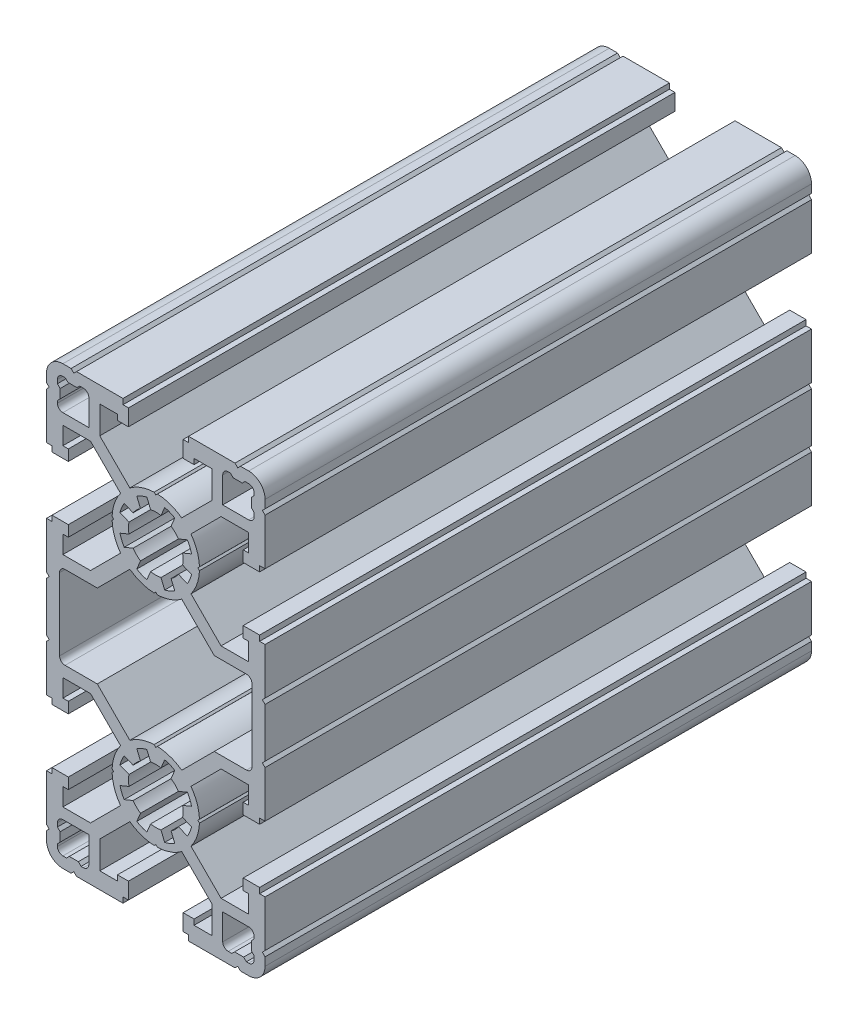
SolidWorks part; units mm, degrees
ref_plane "Ön Düzlem" through (0, 0, 0) normal (0, 0, 1) x (1, 0, 0)
ref_plane "Üst Düzlem" through (0, 0, 0) normal (0, 1, 0) x (1, 0, 0)
ref_plane "Sağ Düzlem" through (0, 0, 0) normal (1, 0, 0) x (0, 0, -1)
ref_plane "Düzlem1" through (0, 0, 100) normal (0, 0, 1) x (1, 0, 0)
sketch "Çizim1" plane through (0, 0, 100) normal (0, 0, 1) x (1, 0, 0)
  line L0 (1.6307, -26.5501) -> (0.9509, -24.9088)
  line L1 (-0.9509, -24.9088) -> (-1.6307, -26.5501)
  line L2 (-3.4785, -25.7847) -> (-2.7986, -24.1434)
  line L3 (-4.1434, -22.7986) -> (-5.7847, -23.4785)
  line L4 (-6.5501, -21.6307) -> (-4.9088, -20.9509)
  line L5 (-4.9088, -19.0491) -> (-6.5501, -18.3693)
  line L6 (-5.7847, -16.5215) -> (-4.1434, -17.2014)
  line L7 (-2.7986, -15.8566) -> (-3.4785, -14.2153)
  line L8 (-1.6307, -13.4499) -> (-0.9509, -15.0912)
  line L9 (0.9509, -15.0912) -> (1.6307, -13.4499)
  line L10 (3.4785, -14.2153) -> (2.7986, -15.8566)
  line L11 (4.1434, -17.2014) -> (5.7847, -16.5215)
  line L12 (6.5501, -18.3693) -> (4.9088, -19.0491)
  line L13 (4.9088, -20.9509) -> (6.5501, -21.6307)
  line L14 (5.7847, -23.4785) -> (4.1434, -22.7986)
  line L15 (2.7986, -24.1434) -> (3.4785, -25.7847)
  line L16 (17, -38) -> (16.5784, -38)
  line L17 (16.5784, -38) -> (16.0784, -37.5)
  line L18 (16.0784, -37.5) -> (14.4216, -37.5)
  line L19 (14.4216, -37.5) -> (13.9216, -38)
  line L20 (13.9216, -38) -> (13.25, -38)
  line L21 (12.25, -37) -> (12.25, -32.25)
  line L22 (12.25, -32.25) -> (17, -32.25)
  line L23 (18, -33.25) -> (18, -33.6716)
  line L24 (18, -33.6716) -> (17.5, -34.1716)
  line L25 (17.5, -34.1716) -> (17.5, -35.8284)
  line L26 (17.5, -35.8284) -> (18, -36.3284)
  line L27 (18, -36.3284) -> (18, -37)
  line L28 (-18, -37) -> (-18, -36.5784)
  line L29 (-18, -36.5784) -> (-17.5, -36.0784)
  line L30 (-17.5, -36.0784) -> (-17.5, -34.4216)
  line L31 (-17.5, -34.4216) -> (-18, -33.9216)
  line L32 (-18, -33.9216) -> (-18, -33.25)
  line L33 (-17, -32.25) -> (-12.25, -32.25)
  line L34 (-12.25, -32.25) -> (-12.25, -37)
  line L35 (-13.25, -38) -> (-13.6716, -38)
  line L36 (-13.6716, -38) -> (-14.1716, -37.5)
  line L37 (-14.1716, -37.5) -> (-15.8284, -37.5)
  line L38 (-15.8284, -37.5) -> (-16.3284, -38)
  line L39 (-16.3284, -38) -> (-17, -38)
  line L40 (5, 36) -> (7, 36)
  line L41 (7, 36) -> (7, 37)
  line L42 (7, 37) -> (10.25, 37)
  line L43 (10.25, 37) -> (10.25, 31.9471)
  line L44 (10.25, 31.9471) -> (4.7443, 26.4414)
  line L45 (0.3064, 27.9941) -> (0, 27.7)
  line L46 (0, 27.7) -> (-0.3064, 27.9941)
  line L47 (-4.7443, 26.4414) -> (-10.25, 31.9471)
  line L48 (-10.25, 31.9471) -> (-10.25, 37)
  line L49 (-10.25, 37) -> (-7, 37)
  line L50 (-7, 37) -> (-7, 36)
  line L51 (-7, 36) -> (-5, 36)
  line L52 (-5, 36) -> (-5, 39)
  line L53 (-5, 39) -> (-6, 39)
  line L54 (-6, 39) -> (-6, 40)
  line L55 (-6, 40) -> (-14.5, 40)
  line L56 (-14.5, 40) -> (-15, 39.5)
  line L57 (-15, 39.5) -> (-15.5, 40)
  line L58 (-15.5, 40) -> (-17, 40)
  line L59 (-20, 37) -> (-20, 35.5)
  line L60 (-20, 35.5) -> (-19.5, 35)
  line L61 (-19.5, 35) -> (-20, 34.5)
  line L62 (-20, 34.5) -> (-20, 26)
  line L63 (-20, 26) -> (-19, 26)
  line L64 (-19, 26) -> (-19, 25)
  line L65 (-19, 25) -> (-16, 25)
  line L66 (-16, 25) -> (-16, 27)
  line L67 (-16, 27) -> (-17, 27)
  line L68 (-17, 27) -> (-17, 30.25)
  line L69 (-17, 30.25) -> (-11.9471, 30.25)
  line L70 (-11.9471, 30.25) -> (-6.4414, 24.7443)
  line L71 (-7.9941, 20.3064) -> (-7.7, 20)
  line L72 (-7.7, 20) -> (-7.9941, 19.6936)
  line L73 (-6.4414, 15.2557) -> (-11.9471, 9.75)
  line L74 (-11.9471, 9.75) -> (-17, 9.75)
  line L75 (-17, 9.75) -> (-17, 13)
  line L76 (-17, 13) -> (-16, 13)
  line L77 (-16, 13) -> (-16, 15)
  line L78 (-16, 15) -> (-19, 15)
  line L79 (-19, 15) -> (-19, 14)
  line L80 (-19, 14) -> (-20, 14)
  line L81 (-20, 14) -> (-20, 5.5)
  line L82 (-20, 5.5) -> (-19.5, 5)
  line L83 (-19.5, 5) -> (-20, 4.5)
  line L84 (-20, 4.5) -> (-20, -4.5)
  line L85 (-20, -4.5) -> (-19.5, -5)
  line L86 (-19.5, -5) -> (-20, -5.5)
  line L87 (-20, -5.5) -> (-20, -14)
  line L88 (-20, -14) -> (-19, -14)
  line L89 (-19, -14) -> (-19, -15)
  line L90 (-19, -15) -> (-16, -15)
  line L91 (-16, -15) -> (-16, -13)
  line L92 (-16, -13) -> (-17, -13)
  line L93 (-17, -13) -> (-17, -9.75)
  line L94 (-17, -9.75) -> (-11.9471, -9.75)
  line L95 (-11.9471, -9.75) -> (-6.4414, -15.2557)
  line L96 (-7.9941, -19.6936) -> (-7.7, -20)
  line L97 (-7.7, -20) -> (-7.9941, -20.3064)
  line L98 (-6.4414, -24.7443) -> (-11.9471, -30.25)
  line L99 (-11.9471, -30.25) -> (-17, -30.25)
  line L100 (-17, -30.25) -> (-17, -27)
  line L101 (-17, -27) -> (-16, -27)
  line L102 (-16, -27) -> (-16, -25)
  line L103 (-16, -25) -> (-19, -25)
  line L104 (-19, -25) -> (-19, -26)
  line L105 (-19, -26) -> (-20, -26)
  line L106 (-20, -26) -> (-20, -34.5)
  line L107 (-20, -34.5) -> (-19.5, -35)
  line L108 (-19.5, -35) -> (-20, -35.5)
  line L109 (-20, -35.5) -> (-20, -37)
  line L110 (-17, -40) -> (-15.5, -40)
  line L111 (-15.5, -40) -> (-15, -39.5)
  line L112 (-15, -39.5) -> (-14.5, -40)
  line L113 (-14.5, -40) -> (-6, -40)
  line L114 (-6, -40) -> (-6, -39)
  line L115 (-6, -39) -> (-5, -39)
  line L116 (-5, -39) -> (-5, -36)
  line L117 (-5, -36) -> (-7, -36)
  line L118 (-7, -36) -> (-7, -37)
  line L119 (-7, -37) -> (-10.25, -37)
  line L120 (-10.25, -37) -> (-10.25, -31.9471)
  line L121 (-10.25, -31.9471) -> (-4.7443, -26.4414)
  line L122 (-0.3064, -27.9941) -> (0, -27.7)
  line L123 (0, -27.7) -> (0.3064, -27.9941)
  line L124 (4.7443, -26.4414) -> (10.25, -31.9471)
  line L125 (10.25, -31.9471) -> (10.25, -37)
  line L126 (10.25, -37) -> (7, -37)
  line L127 (7, -37) -> (7, -36)
  line L128 (7, -36) -> (5, -36)
  line L129 (5, -36) -> (5, -39)
  line L130 (5, -39) -> (6, -39)
  line L131 (6, -39) -> (6, -40)
  line L132 (6, -40) -> (14.5, -40)
  line L133 (14.5, -40) -> (15, -39.5)
  line L134 (15, -39.5) -> (15.5, -40)
  line L135 (15.5, -40) -> (17, -40)
  line L136 (20, -37) -> (20, -35.5)
  line L137 (20, -35.5) -> (19.5, -35)
  line L138 (19.5, -35) -> (20, -34.5)
  line L139 (20, -34.5) -> (20, -26)
  line L140 (20, -26) -> (19, -26)
  line L141 (19, -26) -> (19, -25)
  line L142 (19, -25) -> (16, -25)
  line L143 (16, -25) -> (16, -27)
  line L144 (16, -27) -> (17, -27)
  line L145 (17, -27) -> (17, -30.25)
  line L146 (17, -30.25) -> (11.9471, -30.25)
  line L147 (11.9471, -30.25) -> (6.4414, -24.7443)
  line L148 (7.9941, -20.3064) -> (7.7, -20)
  line L149 (7.7, -20) -> (7.9941, -19.6936)
  line L150 (6.4414, -15.2557) -> (11.9471, -9.75)
  line L151 (11.9471, -9.75) -> (17, -9.75)
  line L152 (17, -9.75) -> (17, -13)
  line L153 (17, -13) -> (16, -13)
  line L154 (16, -13) -> (16, -15)
  line L155 (16, -15) -> (19, -15)
  line L156 (19, -15) -> (19, -14)
  line L157 (19, -14) -> (20, -14)
  line L158 (20, -14) -> (20, -5.5)
  line L159 (20, -5.5) -> (19.5, -5)
  line L160 (19.5, -5) -> (20, -4.5)
  line L161 (20, -4.5) -> (20, 4.5)
  line L162 (20, 4.5) -> (19.5, 5)
  line L163 (19.5, 5) -> (20, 5.5)
  line L164 (20, 5.5) -> (20, 14)
  line L165 (20, 14) -> (19, 14)
  line L166 (19, 14) -> (19, 15)
  line L167 (19, 15) -> (16, 15)
  line L168 (16, 15) -> (16, 13)
  line L169 (16, 13) -> (17, 13)
  line L170 (17, 13) -> (17, 9.75)
  line L171 (17, 9.75) -> (11.9471, 9.75)
  line L172 (11.9471, 9.75) -> (6.4414, 15.2557)
  line L173 (7.9941, 19.6936) -> (7.7, 20)
  line L174 (7.7, 20) -> (7.9941, 20.3064)
  line L175 (6.4414, 24.7443) -> (11.9471, 30.25)
  line L176 (11.9471, 30.25) -> (17, 30.25)
  line L177 (17, 30.25) -> (17, 27)
  line L178 (17, 27) -> (16, 27)
  line L179 (16, 27) -> (16, 25)
  line L180 (16, 25) -> (19, 25)
  line L181 (19, 25) -> (19, 26)
  line L182 (19, 26) -> (20, 26)
  line L183 (20, 26) -> (20, 34.5)
  line L184 (20, 34.5) -> (19.5, 35)
  line L185 (19.5, 35) -> (20, 35.5)
  line L186 (20, 35.5) -> (20, 37)
  line L187 (17, 40) -> (15.5, 40)
  line L188 (15.5, 40) -> (15, 39.5)
  line L189 (15, 39.5) -> (14.5, 40)
  line L190 (14.5, 40) -> (6, 40)
  line L191 (6, 40) -> (6, 39)
  line L192 (6, 39) -> (5, 39)
  line L193 (5, 39) -> (5, 36)
  line L194 (18, 37) -> (18, 36.5784)
  line L195 (18, 36.5784) -> (17.5, 36.0784)
  line L196 (17.5, 36.0784) -> (17.5, 34.4216)
  line L197 (17.5, 34.4216) -> (18, 33.9216)
  line L198 (18, 33.9216) -> (18, 33.25)
  line L199 (17, 32.25) -> (12.25, 32.25)
  line L200 (12.25, 32.25) -> (12.25, 37)
  line L201 (13.25, 38) -> (13.6716, 38)
  line L202 (13.6716, 38) -> (14.1716, 37.5)
  line L203 (14.1716, 37.5) -> (15.8284, 37.5)
  line L204 (15.8284, 37.5) -> (16.3284, 38)
  line L205 (16.3284, 38) -> (17, 38)
  line L206 (-17, 38) -> (-16.5784, 38)
  line L207 (-16.5784, 38) -> (-16.0784, 37.5)
  line L208 (-16.0784, 37.5) -> (-14.4216, 37.5)
  line L209 (-14.4216, 37.5) -> (-13.9216, 38)
  line L210 (-13.9216, 38) -> (-13.25, 38)
  line L211 (-12.25, 37) -> (-12.25, 32.25)
  line L212 (-12.25, 32.25) -> (-17, 32.25)
  line L213 (-18, 33.25) -> (-18, 33.6716)
  line L214 (-18, 33.6716) -> (-17.5, 34.1716)
  line L215 (-17.5, 34.1716) -> (-17.5, 35.8284)
  line L216 (-17.5, 35.8284) -> (-18, 36.3284)
  line L217 (-18, 36.3284) -> (-18, 37)
  line L218 (17.6, 6.6) -> (17.6, -6.6)
  line L219 (16.6, -7.6) -> (10.7029, -7.6)
  line L220 (10.7029, -7.6) -> (4.7443, -13.5586)
  line L221 (0.3064, -12.0059) -> (0, -12.3)
  line L222 (0, -12.3) -> (-0.3064, -12.0059)
  line L223 (-4.7443, -13.5586) -> (-10.7029, -7.6)
  line L224 (-10.7029, -7.6) -> (-16.6, -7.6)
  line L225 (-17.6, -6.6) -> (-17.6, 6.6)
  line L226 (-16.6, 7.6) -> (-10.7029, 7.6)
  line L227 (-10.7029, 7.6) -> (-4.7443, 13.5586)
  line L228 (-0.3064, 12.0059) -> (0, 12.3)
  line L229 (0, 12.3) -> (0.3064, 12.0059)
  line L230 (4.7443, 13.5586) -> (10.7029, 7.6)
  line L231 (10.7029, 7.6) -> (16.6, 7.6)
  line L232 (1.6307, 13.4499) -> (0.9509, 15.0912)
  line L233 (-0.9509, 15.0912) -> (-1.6307, 13.4499)
  line L234 (-3.4785, 14.2153) -> (-2.7986, 15.8566)
  line L235 (-4.1434, 17.2014) -> (-5.7847, 16.5215)
  line L236 (-6.5501, 18.3693) -> (-4.9088, 19.0491)
  line L237 (-4.9088, 20.9509) -> (-6.5501, 21.6307)
  line L238 (-5.7847, 23.4785) -> (-4.1434, 22.7986)
  line L239 (-2.7986, 24.1434) -> (-3.4785, 25.7847)
  line L240 (-1.6307, 26.5501) -> (-0.9509, 24.9088)
  line L241 (0.9509, 24.9088) -> (1.6307, 26.5501)
  line L242 (3.4785, 25.7847) -> (2.7986, 24.1434)
  line L243 (4.1434, 22.7986) -> (5.7847, 23.4785)
  line L244 (6.5501, 21.6307) -> (4.9088, 20.9509)
  line L245 (4.9088, 19.0491) -> (6.5501, 18.3693)
  line L246 (5.7847, 16.5215) -> (4.1434, 17.2014)
  line L247 (2.7986, 15.8566) -> (3.4785, 14.2153)
  arc A0 (3.4785, -25.7847) -> (1.6307, -26.5501) centre (0, -20) cw
  arc A1 (0.9509, -24.9088) -> (-0.9509, -24.9088) centre (0, -20) cw
  arc A2 (-1.6307, -26.5501) -> (-3.4785, -25.7847) centre (0, -20) cw
  arc A3 (-2.7986, -24.1434) -> (-4.1434, -22.7986) centre (0, -20) cw
  arc A4 (-5.7847, -23.4785) -> (-6.5501, -21.6307) centre (0, -20) cw
  arc A5 (-4.9088, -20.9509) -> (-4.9088, -19.0491) centre (0, -20) cw
  arc A6 (-6.5501, -18.3693) -> (-5.7847, -16.5215) centre (0, -20) cw
  arc A7 (-4.1434, -17.2014) -> (-2.7986, -15.8566) centre (0, -20) cw
  arc A8 (-3.4785, -14.2153) -> (-1.6307, -13.4499) centre (0, -20) cw
  arc A9 (-0.9509, -15.0912) -> (0.9509, -15.0912) centre (0, -20) cw
  arc A10 (1.6307, -13.4499) -> (3.4785, -14.2153) centre (0, -20) cw
  arc A11 (2.7986, -15.8566) -> (4.1434, -17.2014) centre (0, -20) cw
  arc A12 (5.7847, -16.5215) -> (6.5501, -18.3693) centre (0, -20) cw
  arc A13 (4.9088, -19.0491) -> (4.9088, -20.9509) centre (0, -20) cw
  arc A14 (6.5501, -21.6307) -> (5.7847, -23.4785) centre (0, -20) cw
  arc A15 (4.1434, -22.7986) -> (2.7986, -24.1434) centre (0, -20) cw
  arc A16 (13.25, -38) -> (12.25, -37) centre (13.25, -37) cw
  arc A17 (17, -32.25) -> (18, -33.25) centre (17, -33.25) cw
  arc A18 (18, -37) -> (17, -38) centre (17, -37) cw
  arc A19 (-18, -33.25) -> (-17, -32.25) centre (-17, -33.25) cw
  arc A20 (-12.25, -37) -> (-13.25, -38) centre (-13.25, -37) cw
  arc A21 (-17, -38) -> (-18, -37) centre (-17, -37) cw
  arc A22 (4.7443, 26.4414) -> (0.3064, 27.9941) centre (0, 20) ccw
  arc A23 (-0.3064, 27.9941) -> (-4.7443, 26.4414) centre (0, 20) ccw
  arc A24 (-17, 40) -> (-20, 37) centre (-17, 37) ccw
  arc A25 (-6.4414, 24.7443) -> (-7.9941, 20.3064) centre (0, 20) ccw
  arc A26 (-7.9941, 19.6936) -> (-6.4414, 15.2557) centre (0, 20) ccw
  arc A27 (-6.4414, -15.2557) -> (-7.9941, -19.6936) centre (0, -20) ccw
  arc A28 (-7.9941, -20.3064) -> (-6.4414, -24.7443) centre (0, -20) ccw
  arc A29 (-20, -37) -> (-17, -40) centre (-17, -37) ccw
  arc A30 (-4.7443, -26.4414) -> (-0.3064, -27.9941) centre (0, -20) ccw
  arc A31 (0.3064, -27.9941) -> (4.7443, -26.4414) centre (0, -20) ccw
  arc A32 (17, -40) -> (20, -37) centre (17, -37) ccw
  arc A33 (6.4414, -24.7443) -> (7.9941, -20.3064) centre (0, -20) ccw
  arc A34 (7.9941, -19.6936) -> (6.4414, -15.2557) centre (0, -20) ccw
  arc A35 (6.4414, 15.2557) -> (7.9941, 19.6936) centre (0, 20) ccw
  arc A36 (7.9941, 20.3064) -> (6.4414, 24.7443) centre (0, 20) ccw
  arc A37 (20, 37) -> (17, 40) centre (17, 37) ccw
  arc A38 (18, 33.25) -> (17, 32.25) centre (17, 33.25) cw
  arc A39 (12.25, 37) -> (13.25, 38) centre (13.25, 37) cw
  arc A40 (17, 38) -> (18, 37) centre (17, 37) cw
  arc A41 (-13.25, 38) -> (-12.25, 37) centre (-13.25, 37) cw
  arc A42 (-17, 32.25) -> (-18, 33.25) centre (-17, 33.25) cw
  arc A43 (-18, 37) -> (-17, 38) centre (-17, 37) cw
  arc A44 (17.6, -6.6) -> (16.6, -7.6) centre (16.6, -6.6) cw
  arc A45 (4.7443, -13.5586) -> (0.3064, -12.0059) centre (0, -20) ccw
  arc A46 (-0.3064, -12.0059) -> (-4.7443, -13.5586) centre (0, -20) ccw
  arc A47 (-16.6, -7.6) -> (-17.6, -6.6) centre (-16.6, -6.6) cw
  arc A48 (-17.6, 6.6) -> (-16.6, 7.6) centre (-16.6, 6.6) cw
  arc A49 (-4.7443, 13.5586) -> (-0.3064, 12.0059) centre (0, 20) ccw
  arc A50 (0.3064, 12.0059) -> (4.7443, 13.5586) centre (0, 20) ccw
  arc A51 (16.6, 7.6) -> (17.6, 6.6) centre (16.6, 6.6) cw
  arc A52 (3.4785, 14.2153) -> (1.6307, 13.4499) centre (0, 20) cw
  arc A53 (0.9509, 15.0912) -> (-0.9509, 15.0912) centre (0, 20) cw
  arc A54 (-1.6307, 13.4499) -> (-3.4785, 14.2153) centre (0, 20) cw
  arc A55 (-2.7986, 15.8566) -> (-4.1434, 17.2014) centre (0, 20) cw
  arc A56 (-5.7847, 16.5215) -> (-6.5501, 18.3693) centre (0, 20) cw
  arc A57 (-4.9088, 19.0491) -> (-4.9088, 20.9509) centre (0, 20) cw
  arc A58 (-6.5501, 21.6307) -> (-5.7847, 23.4785) centre (0, 20) cw
  arc A59 (-4.1434, 22.7986) -> (-2.7986, 24.1434) centre (0, 20) cw
  arc A60 (-3.4785, 25.7847) -> (-1.6307, 26.5501) centre (0, 20) cw
  arc A61 (-0.9509, 24.9088) -> (0.9509, 24.9088) centre (0, 20) cw
  arc A62 (1.6307, 26.5501) -> (3.4785, 25.7847) centre (0, 20) cw
  arc A63 (2.7986, 24.1434) -> (4.1434, 22.7986) centre (0, 20) cw
  arc A64 (5.7847, 23.4785) -> (6.5501, 21.6307) centre (0, 20) cw
  arc A65 (4.9088, 20.9509) -> (4.9088, 19.0491) centre (0, 20) cw
  arc A66 (6.5501, 18.3693) -> (5.7847, 16.5215) centre (0, 20) cw
  arc A67 (4.1434, 17.2014) -> (2.7986, 15.8566) centre (0, 20) cw
extrude "Yükseklik-Ekstrüzyon1" add sketch "Çizim1" against normal blind 100
